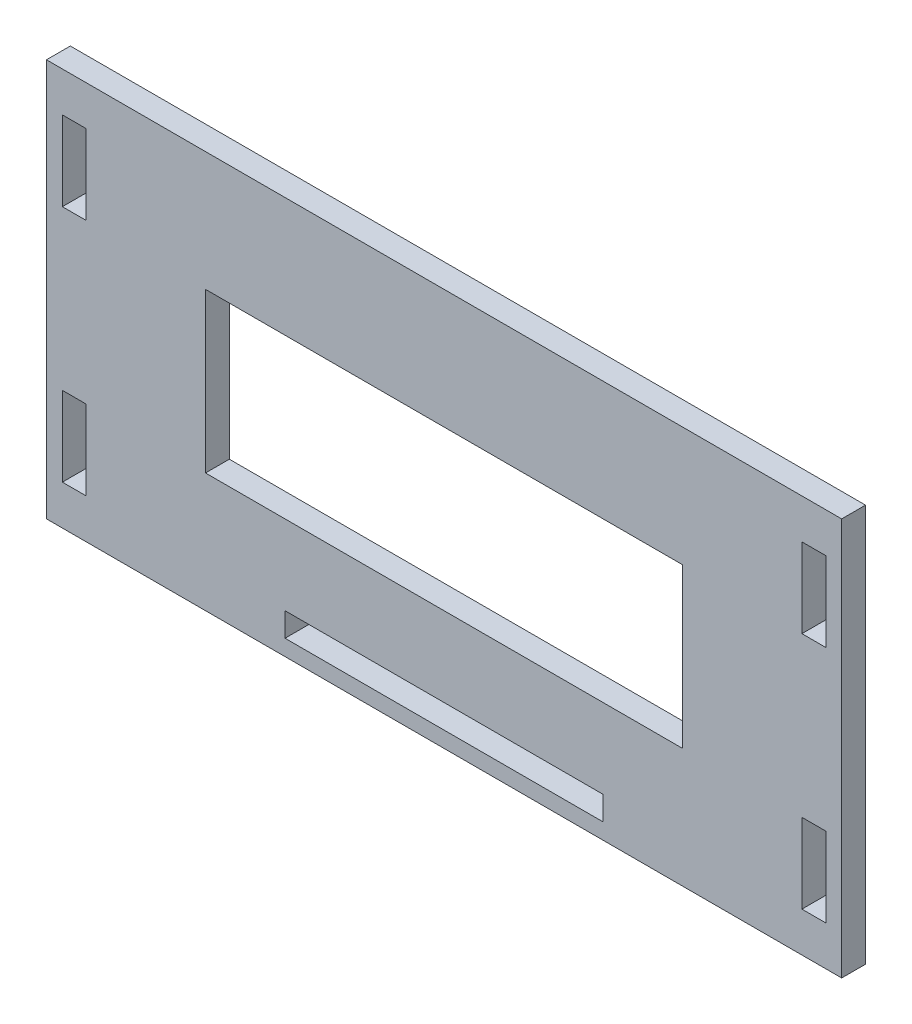
SolidWorks part; units mm, degrees
ref_plane "Front Plane" through (0, 0, 0) normal (0, 0, 1) x (1, 0, 0)
ref_plane "Top Plane" through (0, 0, 0) normal (0, 1, 0) x (1, 0, 0)
ref_plane "Right Plane" through (0, 0, 0) normal (1, 0, 0) x (0, 0, -1)
sketch "Sketch3" plane through (0, 0, 0) normal (0, 0, 1) x (1, 0, 0)
  line L1 (50, 25) -> (-50, 25)
  line L2 (50, 25) -> (50, -25)
  line L3 (50, -25) -> (-50, -25)
  line L4 (-50, 25) -> (-50, -25)
  line L5 (-20, -20) -> (20, -20)
  line L6 (-20, -20) -> (-20, -23)
  line L11 (-48, 20) -> (-45, 20)
  line L12 (-48, 20) -> (-48, 10)
  line L13 (-48, 10) -> (-45, 10)
  line L14 (-45, 20) -> (-45, 10)
  line L15 (-20, -23) -> (20, -23)
  line L16 (20, -20) -> (20, -23)
  line L17 (30, 10) -> (-30, 10)
  line L20 (45, 20) -> (45, 10)
  line L21 (48, 10) -> (45, 10)
  line L22 (48, 20) -> (48, 10)
  line L23 (48, 20) -> (45, 20)
  line L26 (48, -20) -> (45, -20)
  line L27 (48, -20) -> (48, -10)
  line L28 (48, -10) -> (45, -10)
  line L29 (45, -20) -> (45, -10)
  line L32 (-45, -20) -> (-45, -10)
  line L33 (-48, -10) -> (-45, -10)
  line L34 (-48, -20) -> (-48, -10)
  line L35 (-48, -20) -> (-45, -20)
  line L36 (30, 10) -> (30, -10)
  line L37 (30, -10) -> (-30, -10)
  line L38 (-30, 10) -> (-30, -10)
  dimension "D1" = 100
  dimension "D2" = 50
  dimension "D3" = 60
  dimension "D4" = 20
  dimension "D5" = 40
  dimension "D6" = 3
extrude "Boss-Extrude2" add sketch "Sketch3" along normal blind 3
